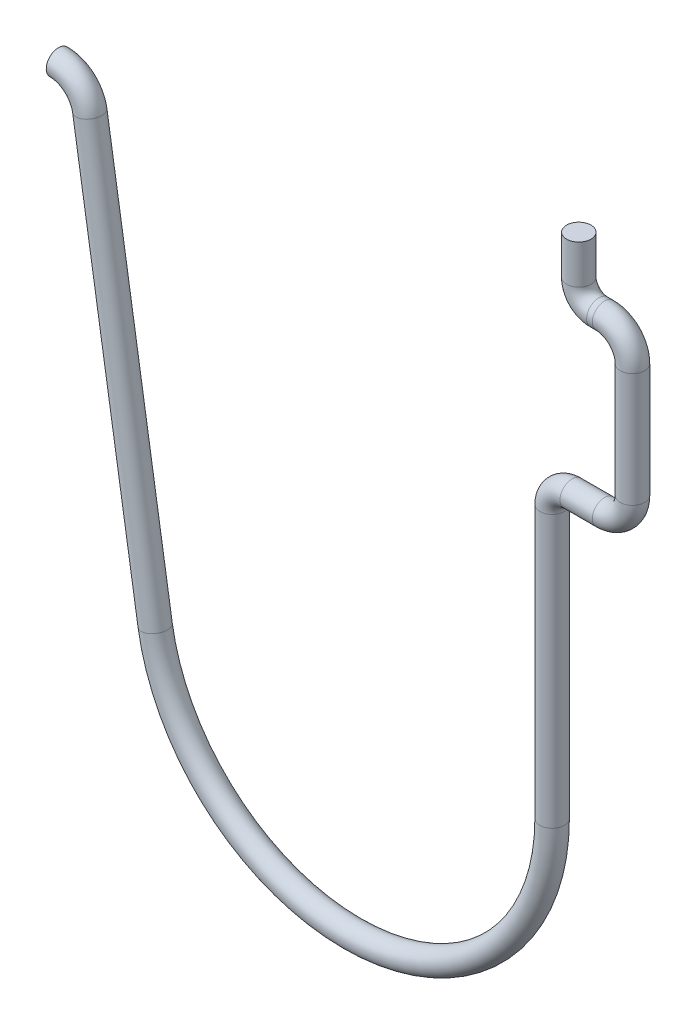
SolidWorks part; units mm, degrees
ref_plane "Front Plane" through (0, 0, 0) normal (0, 0, 1) x (1, 0, 0)
ref_plane "Top Plane" through (0, 0, 0) normal (0, 1, 0) x (1, 0, 0)
ref_plane "Right Plane" through (0, 0, 0) normal (1, 0, 0) x (0, 0, -1)
sketch "Sketch1" plane through (0, 0, 0) normal (0, 0, 1) x (1, 0, 0)
  line L0 (-31.7942, -9.0645) -> (-27.5426, -35.9078)
  line L1 (-1.7331, -33.8766) -> (-1.7331, -16.2052)
  line L2 (-0.4314, -14.9034) -> (1.67, -14.9035)
  line L3 (3.4925, -13.081) -> (3.4925, -5.6642)
  line L4 (1.67, -3.8418) -> (1.3017, -3.8418)
  line L5 (0, -2.54) -> (0, 0)
  arc A0 (-31.7942, -9.0645) -> (-33.8325, -7.3235) centre (-33.8325, -9.3873) ccw
  arc A1 (-27.5426, -35.9078) -> (-1.7331, -33.8766) centre (-14.7178, -33.8766) ccw
  arc A2 (-0.4314, -14.9034) -> (-1.7331, -16.2052) centre (-0.4314, -16.2052) ccw
  arc A3 (1.67, -14.9035) -> (3.4925, -13.081) centre (1.67, -13.081) ccw
  arc A4 (3.4925, -5.6642) -> (1.67, -3.8418) centre (1.67, -5.6642) ccw
  arc A5 (0, -2.54) -> (1.3017, -3.8418) centre (1.3017, -2.54) ccw
  dimension "D2" = 2.0637
  dimension "D7" = 12.9847
  dimension "D1" = 9
  dimension "D3" = 27.178
  dimension "D4" = 0
  dimension "D5" = 33.8766
  dimension "D6" = 14.7178
sketch "Sketch2" plane through (0, 0, 0) normal (0, 1, 0) x (1, 0, 0)
  circle A0 centre (0, 0) radius 0.7937
  dimension "D1" = 1.5875
sweep "Sweep1" add profiles "Sketch2" path "Sketch1"
